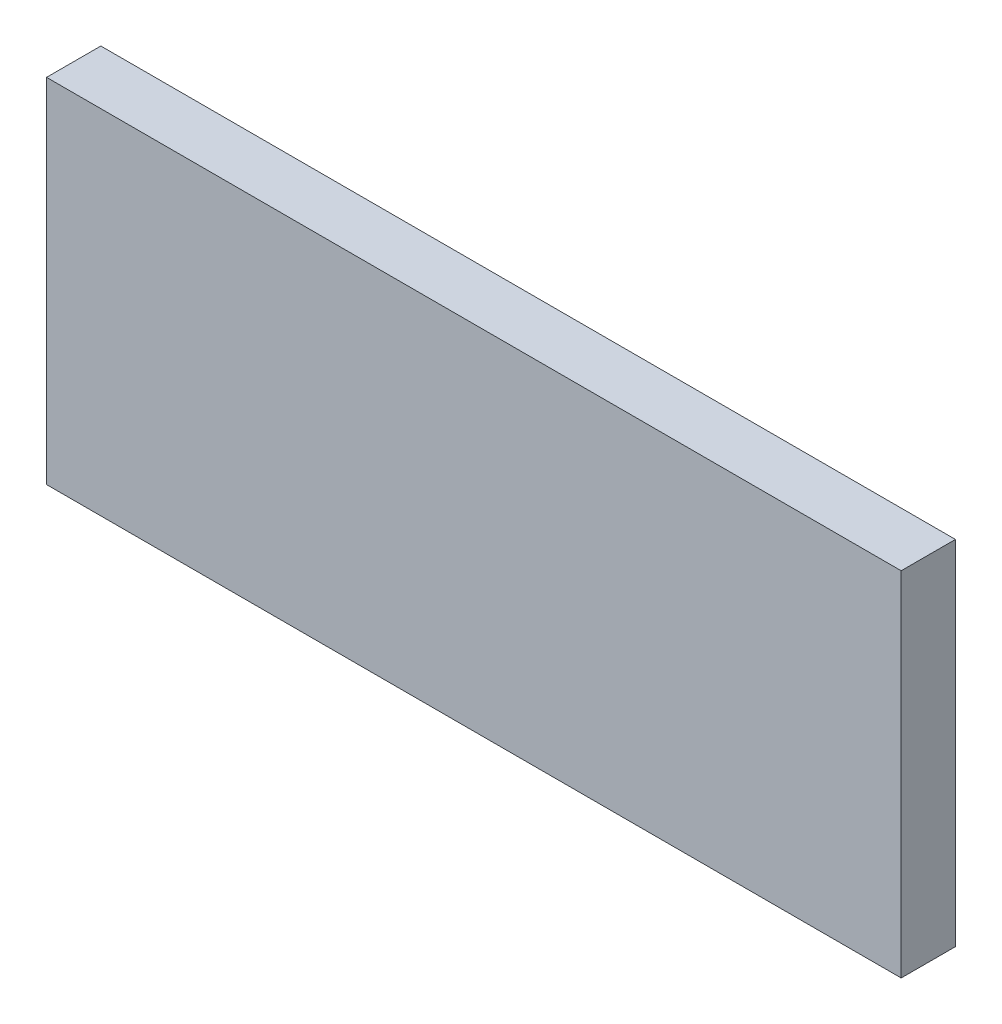
SolidWorks part; units mm, degrees
ref_plane "Ön Düzlem" through (0, 0, 0) normal (0, 0, 1) x (1, 0, 0)
ref_plane "Üst Düzlem" through (0, 0, 0) normal (0, 1, 0) x (1, 0, 0)
ref_plane "Sağ Düzlem" through (0, 0, 0) normal (1, 0, 0) x (0, 0, -1)
sketch "Sketch1" plane through (0, 0, 0) normal (0, 0, 1) x (1, 0, 0)
  line L1 (-33.6009, 9.3509) -> (29.3991, 9.3509)
  line L2 (-33.6009, 9.3509) -> (-33.6009, -16.6491)
  line L3 (-33.6009, -16.6491) -> (29.3991, -16.6491)
  line L4 (29.3991, 9.3509) -> (29.3991, -16.6491)
  dimension "D1" = 26
  dimension "D2" = 63
extrude "Boss-Extrude1" add sketch "Sketch1" along normal blind 4
